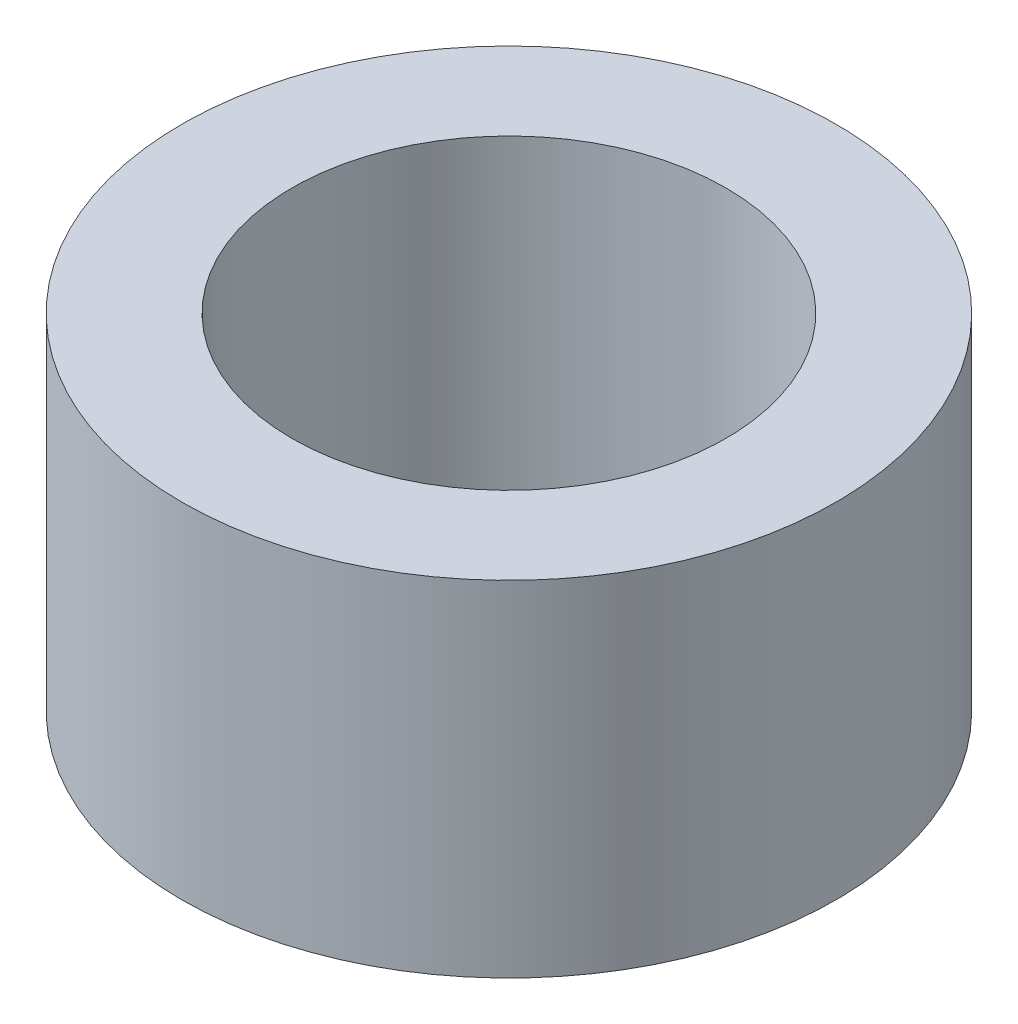
SolidWorks part; units mm, degrees
material "Cardboard"
ref_plane "Frontal Plane" through (0, 0, 0) normal (0, 0, 1) x (1, 0, 0)
ref_plane "Horizontal Plane" through (0, 0, 0) normal (0, 1, 0) x (1, 0, 0)
ref_plane "Profile Plane" through (0, 0, 0) normal (1, 0, 0) x (0, 0, -1)
sketch "Sketch1" plane through (0, 0, 0) normal (0, 1, 0) x (1, 0, 0)
  circle A0 centre (0, 0) radius 6.3
  circle A1 centre (0, 0) radius 9.5
  dimension "D1" = 12.6
  dimension "D2" = 19
extrude "Boss-Extrude1" add sketch "Sketch1" along normal blind 10
